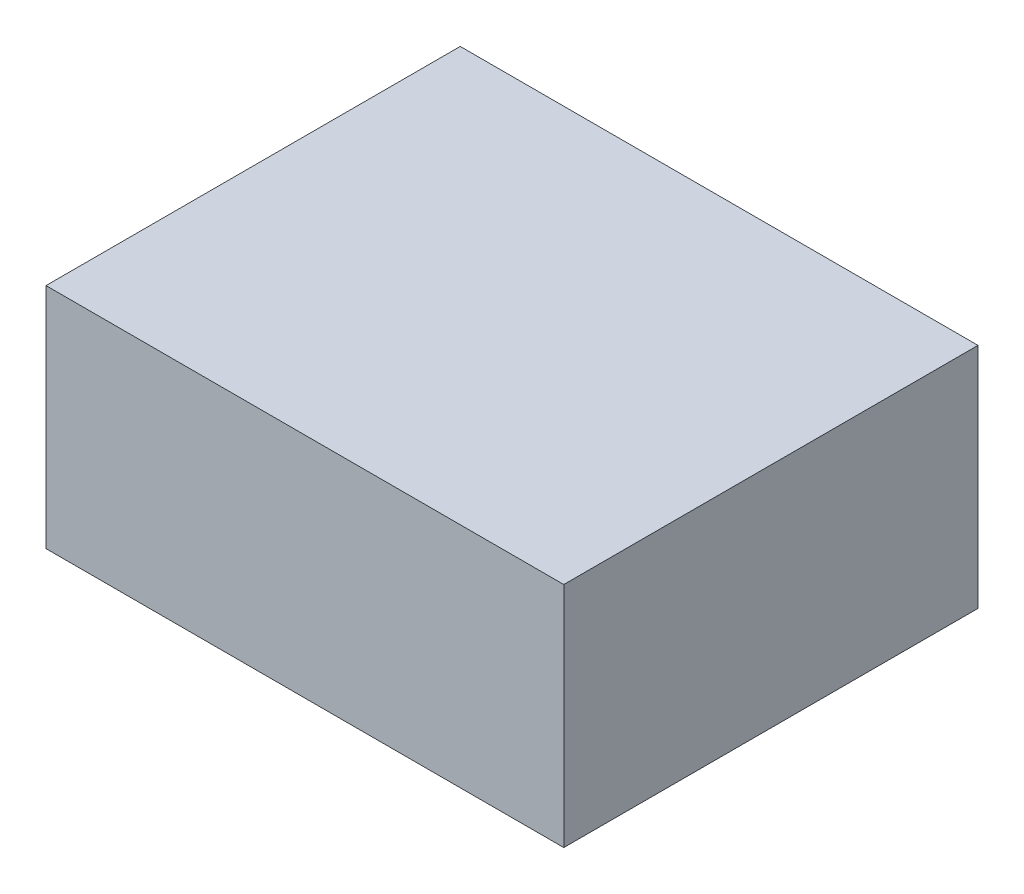
SolidWorks part; units mm, degrees
material "ABS"
ref_plane "Front Plane" through (0, 0, 0) normal (0, 0, 1) x (1, 0, 0)
ref_plane "Top Plane" through (0, 0, 0) normal (0, 1, 0) x (1, 0, 0)
ref_plane "Right Plane" through (0, 0, 0) normal (1, 0, 0) x (0, 0, -1)
sketch "Sketch1" plane through (0, 0, 0) normal (0, 1, 0) x (1, 0, 0)
  line L0 (-2.5, 2) -> (2.5, -2) construction
  line L1 (-2.5, 2) -> (2.5, 2)
  line L2 (-2.5, 2) -> (-2.5, -2)
  line L3 (-2.5, -2) -> (2.5, -2)
  line L4 (2.5, 2) -> (2.5, -2)
  dimension "D1" = 5
  dimension "D2" = 4
extrude "Boss-Extrude1" add sketch "Sketch1" along normal blind 2.2
